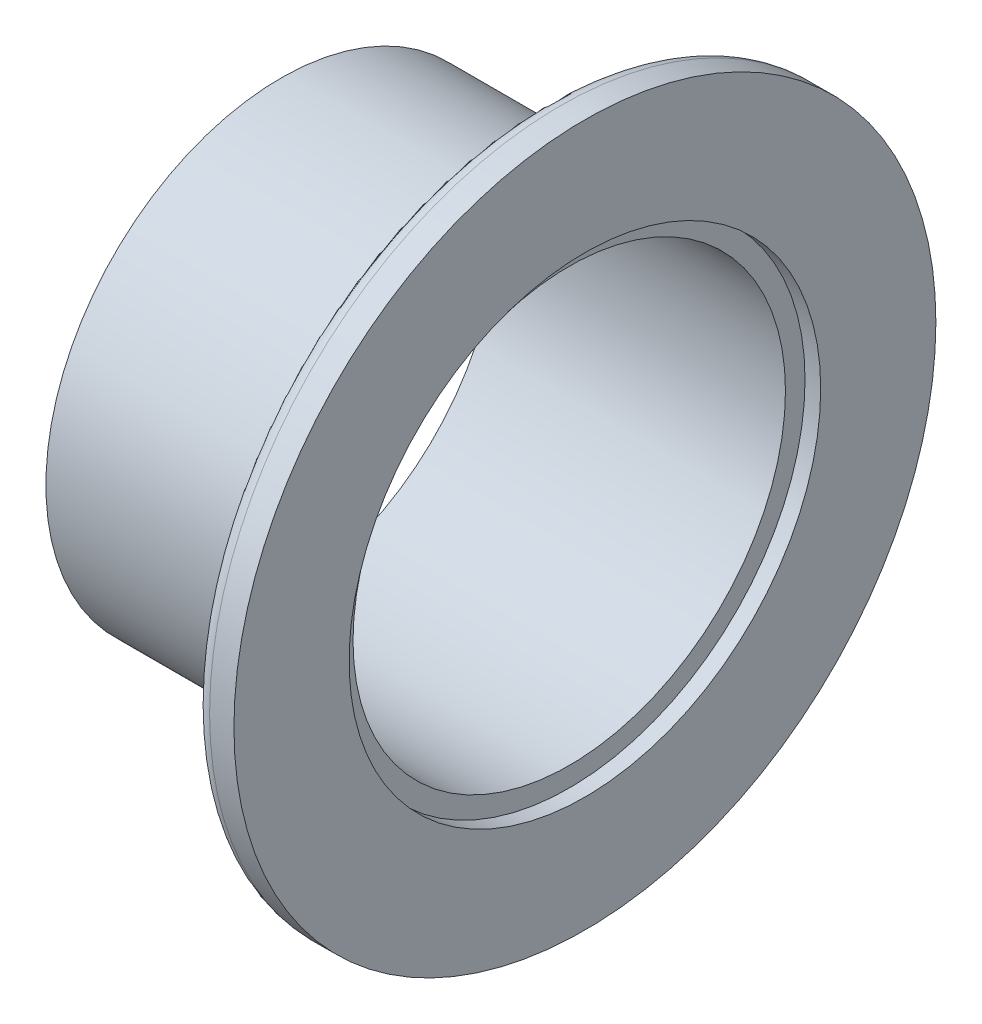
SolidWorks part; units mm, degrees
ref_plane "Front Plane" through (0, 0, 0) normal (0, 0, 1) x (1, 0, 0)
ref_plane "Top Plane" through (0, 0, 0) normal (0, 1, 0) x (1, 0, 0)
ref_plane "Right Plane" through (0, 0, 0) normal (1, 0, 0) x (0, 0, -1)
sketch "Sketch1" plane through (0, 0, 0) normal (1, 0, 0) x (0, 0, -1)
  circle A0 centre (0, 0) radius 19.05
  circle A1 centre (0, 0) radius 17.526
  dimension "D1" = 35.052
  dimension "D2" = 38.1
extrude "Boss-Extrude1" add sketch "Sketch1" along normal blind 19.05
sketch "Sketch2" plane through (19.05, 0, 0) normal (1, 0, 0) x (0, 0, -1)
  circle A0 centre (0, 0) radius 28.448
  dimension "D1" = 56.896
extrude "Boss-Extrude2" add sketch "Sketch2" along normal blind 5.588
chamfer "Chamfer1" distance 7.493 angle 20 1 edges at (19.05, 0, -28.448)
fillet "Fillet2" radius 1.27 1 edges at (21.7772, 0, -28.448)
sketch "Sketch3" plane through (19.05, 0, 0) normal (-1, 0, 0) x (0, 0, 1)
  circle A0 centre (0, 0) radius 17.526
extrude "Cut-Extrude1" cut sketch "Sketch3" against normal through all
sketch "Sketch4" plane through (24.638, 0, 0) normal (1, 0, 0) x (0, 0, -1)
  circle A0 centre (0, 0) radius 19.1135
  circle A1 centre (0, 0) radius 17.526
extrude "Cut-Extrude2" cut sketch "Sketch4" against normal blind 1.27
